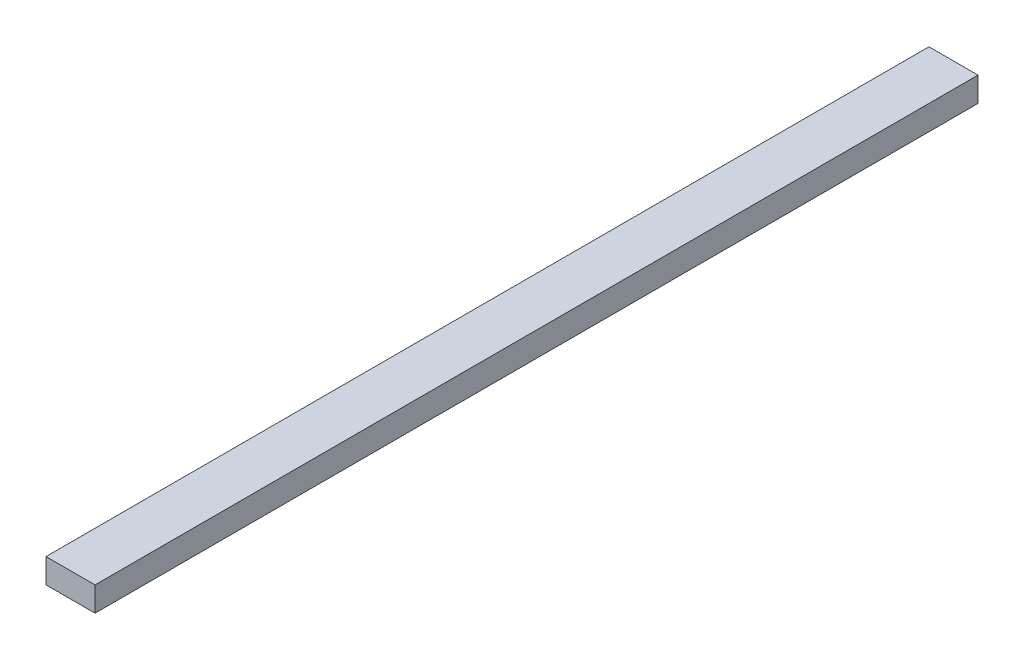
SolidWorks part; units mm, degrees
material "Pink Foam"
ref_plane "Front Plane" through (0, 0, 0) normal (0, 0, 1) x (1, 0, 0)
ref_plane "Top Plane" through (0, 0, 0) normal (0, 1, 0) x (1, 0, 0)
ref_plane "Right Plane" through (0, 0, 0) normal (1, 0, 0) x (0, 0, -1)
sketch "Sketch1" plane through (0, 0, 0) normal (0, 0, 1) x (1, 0, 0)
  line L1 (-25.4, -12.7) -> (25.4, -12.7)
  line L2 (-25.4, -12.7) -> (-25.4, 12.7)
  line L3 (-25.4, 12.7) -> (25.4, 12.7)
  line L4 (25.4, -12.7) -> (25.4, 12.7)
  line L5 (-25.4, -12.7) -> (25.4, 12.7) construction
  line L6 (-25.4, 12.7) -> (25.4, -12.7) construction
  point P0 (0, 0)
  dimension "D1" = 25.4
  dimension "D2" = 50.8
extrude "Boss-Extrude1" add sketch "Sketch1" along normal blind 914.4
